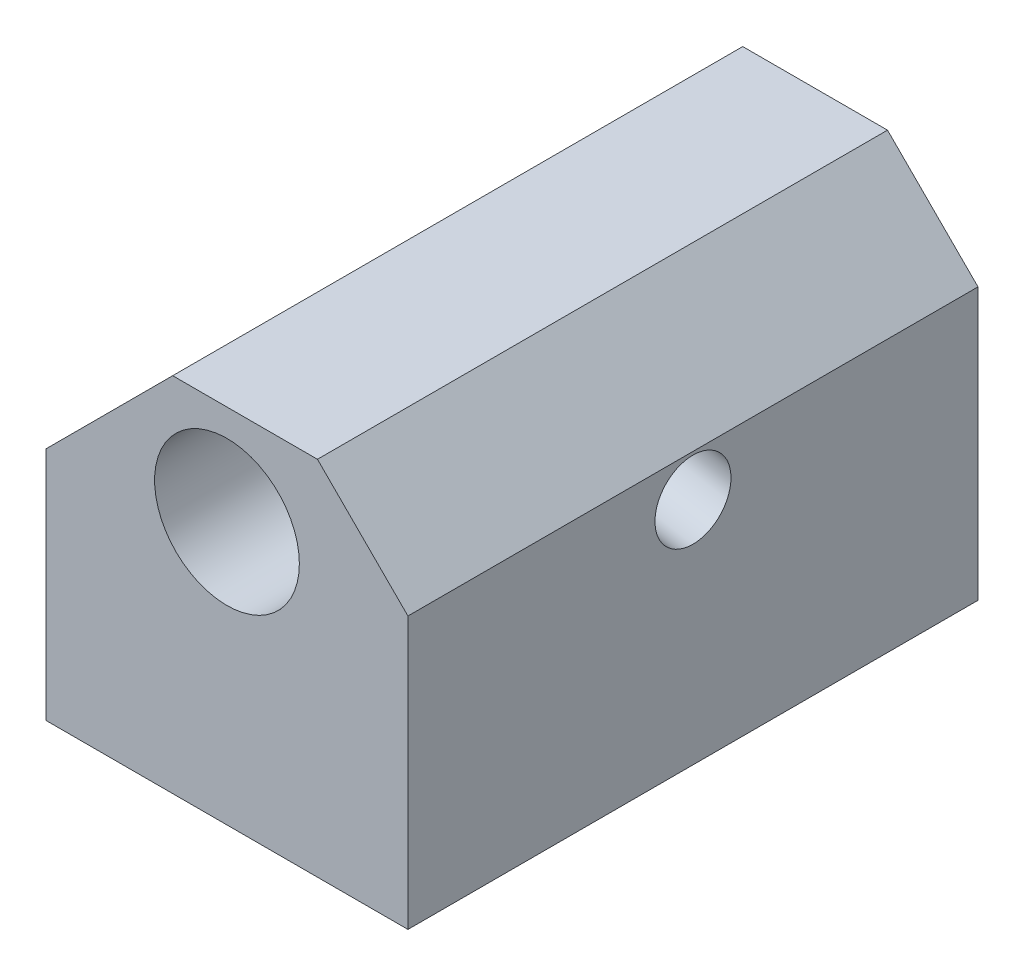
SolidWorks part; units mm, degrees
material "XC38"
ref_plane "Face" through (0, 0, 0) normal (0, 0, 1) x (1, 0, 0)
ref_plane "Dessus" through (0, 0, 0) normal (0, 1, 0) x (1, 0, 0)
ref_plane "Droite" through (0, 0, 0) normal (1, 0, 0) x (0, 0, -1)
sketch "Esquisse1" plane through (0, 0, 0) normal (0, 0, 1) x (1, 0, 0)
  line L0 (-10, 3) -> (-10, -10)
  line L1 (10, 5) -> (10, -10)
  line L2 (10, -10) -> (-10, -10)
  line L3 (0, 10) -> (0, 8.5) construction
  line L4 (0, 0) -> (0, -10) construction
  line L5 (10, 5) -> (5, 10)
  line L6 (5, 10) -> (-3, 10)
  line L7 (-3, 10) -> (-10, 3)
  circle A1 centre (0, 4.5) radius 4
  point P1 (0, 10)
  dimension "D3" = 8
  dimension "D1" = 20
  dimension "D2" = 20
  dimension "D4" = 1.5
  dimension "D5" = 10
  dimension "D6" = 13
  dimension "D7" = 15
  dimension "D8" = 45
extrude "Boss.-Extru.1" add sketch "Esquisse1" along normal mid plane 31.5
hole_wizard "Trou taraudé M101" positions "Esquisse3" profile "Esquisse2" tap size "M10" standard "ISO"
sketch "Esquisse3" plane through (0, -10, 0) normal (0, -1, 0) x (-1, 0, 0)
  point P0 (0, 0)
sketch "Esquisse2" plane through (0, -10, 0) normal (1, 0, 0) x (0, 0, -1)
  line L0 (0, 0) -> (0, 17.5537)
  line L1 (0, 17.5537) -> (4.25, 15)
  line L2 (4.25, 15) -> (4.25, 0)
  line L5 (4.25, 0) -> (0, 0)
  line L10 (0, 17.5537) -> (-4.25, 15) construction
  line L11 (0, -6.35) -> (0, 107.95) construction
  dimension "Diamètre du trou pour taraudage" = 8.5
  dimension "Profondeur du trou pour taraudage" = 15
  dimension "Angle de pointe" = 118
cosmetic thread "Filetage de perçage1" parameters "D1"=11, "D2"=10
ref_plane "Plan1" through (11.4086, -2.0116, 0) normal (-0.9848, 0.1736, 0) x (0, 0, -1)
hole_wizard "Trou taraudé M51" positions "Esquisse5" profile "Esquisse4" tap size "M5" standard "ISO"
sketch "Esquisse5" plane through (11.4086, -2.0116, 0) normal (-0.9848, 0.1736, 0) x (0, 0, -1)
  line L1 (-15.75, 8.1116) -> (15.75, 8.1116) construction
  point P0 (0, -4.3884)
  dimension "D1" = 12.5
sketch "Esquisse4" plane through (12.1706, 2.3101, 0) normal (0, 0, 1) x (0.1736, 0.9848, 0)
  line L0 (0, 0) -> (0, 11.2618)
  line L1 (0, 11.2618) -> (2.1, 10)
  line L2 (2.1, 10) -> (2.1, 0)
  line L5 (2.1, 0) -> (0, 0)
  line L10 (0, 11.2618) -> (-2.1, 10) construction
  line L11 (0, -6.35) -> (0, 107.95) construction
  dimension "Diamètre du trou pour taraudage" = 4.2
  dimension "Profondeur du trou pour taraudage" = 10
  dimension "Angle de pointe" = 118
cosmetic thread "Filetage de perçage3" parameters "D1"=7.1371, "D2"=5
